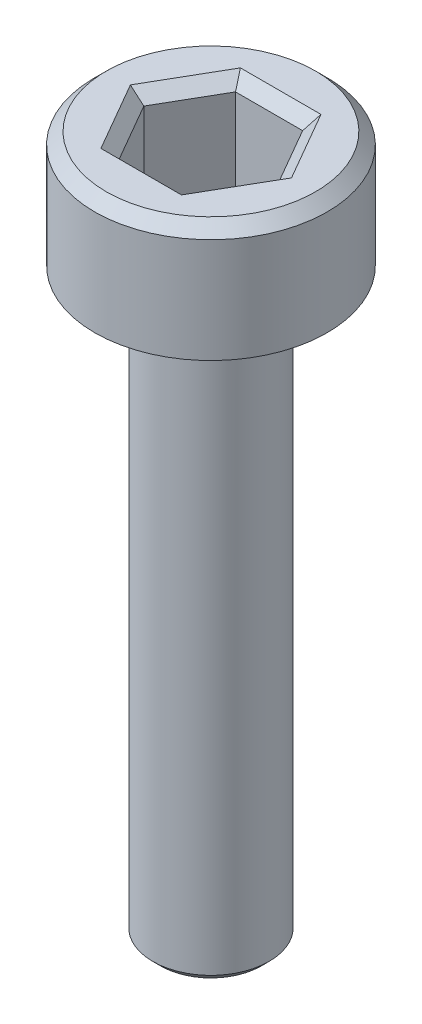
SolidWorks part; units mm, degrees
ref_plane "Front Plane" through (0, 0, 0) normal (0, 0, 1) x (1, 0, 0)
ref_plane "Top Plane" through (0, 0, 0) normal (0, 1, 0) x (1, 0, 0)
ref_plane "Right Plane" through (0, 0, 0) normal (1, 0, 0) x (0, 0, -1)
sketch "Sketch1" plane through (0, 0, 0) normal (0, 1, 0) x (1, 0, 0)
  circle A0 centre (0, 0) radius 3
  dimension "D1" = 6
extrude "Boss-Extrude1" add sketch "Sketch1" along normal blind 3
chamfer "Chamfer1" distance 0.3 angle 45 1 edges at (0, 3, 3)
sketch "Sketch2" plane through (0, 3, 0) normal (0, 1, 0) x (1, 0, 0)
  line L1 (1.7321, 0) -> (0.866, 1.5)
  line L2 (0.866, 1.5) -> (-0.866, 1.5)
  line L3 (-0.866, 1.5) -> (-1.7321, 0)
  line L4 (-1.7321, 0) -> (-0.866, -1.5)
  line L5 (-0.866, -1.5) -> (0.866, -1.5)
  line L6 (0.866, -1.5) -> (1.7321, 0)
  circle A0 centre (0, 0) radius 1.5 construction
  dimension "D1" = 3
extrude "Cut-Extrude1" cut sketch "Sketch2" against normal blind 2.5
chamfer "Chamfer2" distance 0.3 angle 45 6 edges at (1.299, 3, -0.75) (1.299, 3, 0.75) (0, 3, 1.5) (-1.299, 3, 0.75) (-1.299, 3, -0.75) (0, 3, -1.5)
sketch "Sketch3" plane through (0, 0, 0) normal (0, -1, 0) x (1, 0, 0)
  circle A0 centre (0, 0) radius 1.5
  dimension "D1" = 3
extrude "Boss-Extrude2" add sketch "Sketch3" along normal blind 15
chamfer "Chamfer3" distance 0.2 angle 45 1 edges at (0, -15, -1.5)
